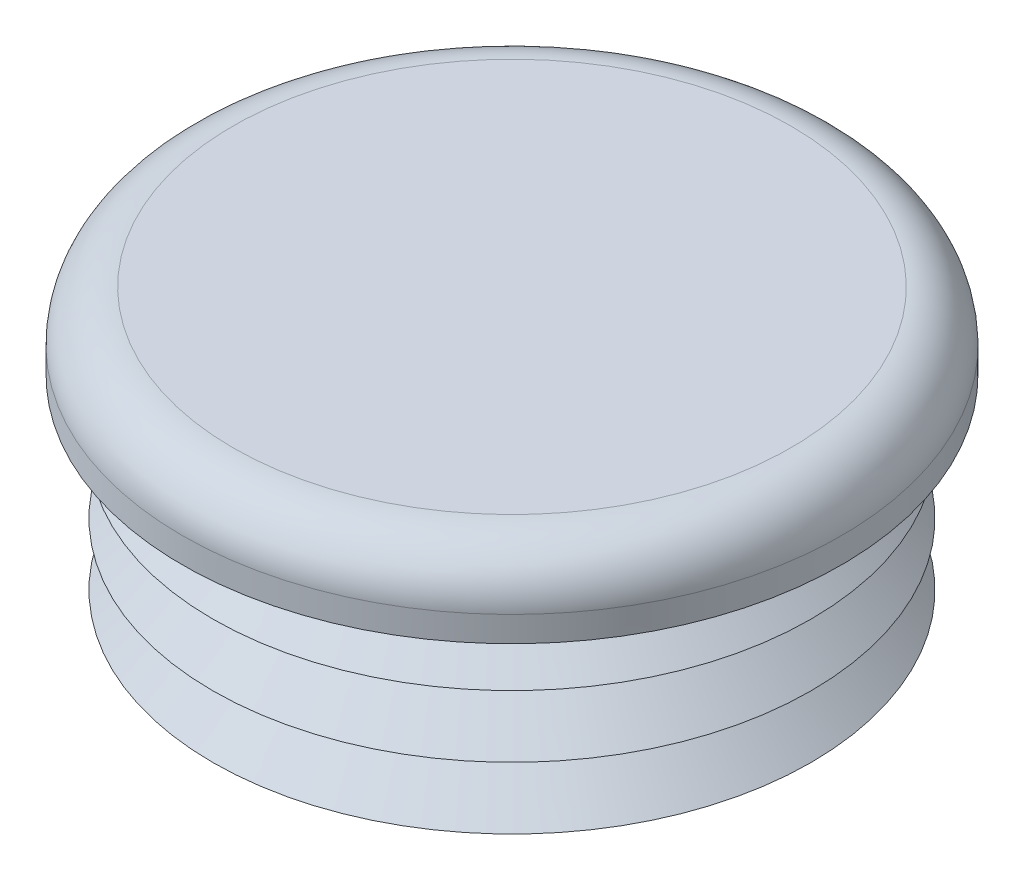
SolidWorks part; units mm, degrees
ref_plane "Front Plane" through (0, 0, 0) normal (0, 0, 1) x (1, 0, 0)
ref_plane "Top Plane" through (0, 0, 0) normal (0, 1, 0) x (1, 0, 0)
ref_plane "Right Plane" through (0, 0, 0) normal (1, 0, 0) x (0, 0, -1)
sketch "Sketch1" plane through (0, 0, 0) normal (0, 0, 1) x (1, 0, 0)
  line L0 (0, 0) -> (0, 12.7) construction
  line L1 (0, 12.7) -> (0, 17.4625) construction
  line L2 (15.875, 0) -> (15.875, 1.0319)
  line L3 (15.875, 1.0319) -> (18.7325, 1.0319)
  line L4 (18.7325, 1.0319) -> (15.875, 3.8894)
  line L5 (15.875, 3.8894) -> (15.875, 4.9213)
  line L6 (15.875, 4.9213) -> (18.7325, 4.9213)
  line L7 (18.7325, 4.9213) -> (15.875, 7.7787)
  line L8 (15.875, 7.7787) -> (15.875, 8.8106)
  line L9 (15.875, 8.8106) -> (18.7325, 8.8106)
  line L10 (18.7325, 8.8106) -> (15.875, 11.6681)
  line L11 (15.875, 11.6681) -> (15.875, 12.7)
  line L12 (15.875, 12.7) -> (20.6375, 12.7)
  line L13 (20.6375, 12.7) -> (20.6375, 17.4625)
  line L14 (20.6375, 17.4625) -> (0, 17.4625)
  line L15 (0, 12.7) -> (14.9225, 12.7)
  line L16 (14.9225, 12.7) -> (14.9225, 0)
  line L17 (14.9225, 0) -> (15.875, 0)
  line L18 (0, 12.7) -> (0, 17.4625)
  dimension "D1" = 12.7
  dimension "D2" = 4.7625
  dimension "D3" = 37.465
  dimension "D4" = 31.75
  dimension "D5" = 45
  dimension "D6" = 29.845
  dimension "D7" = 41.275
revolve "Revolve1" add sketch "Sketch1" angle 360 about L0
fillet "Fillet1" radius 3.175 1 edges at (0, 17.4625, -20.6375)
